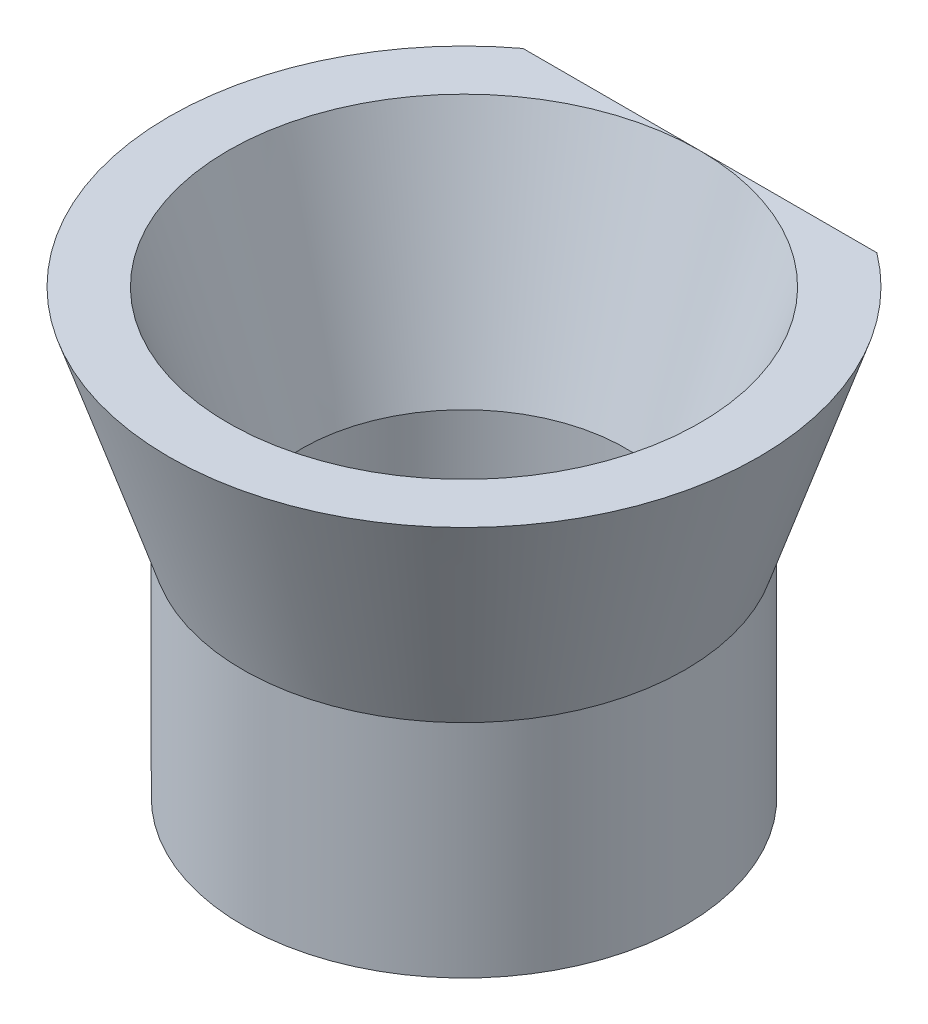
SolidWorks part; units mm, degrees
ref_plane "Alzado" through (0, 0, 0) normal (0, 0, 1) x (1, 0, 0)
ref_plane "Planta" through (0, 0, 0) normal (0, 1, 0) x (1, 0, 0)
ref_plane "Vista lateral" through (0, 0, 0) normal (1, 0, 0) x (0, 0, -1)
sketch "Croquis2" plane through (0, 0, 0) normal (0, 0, 1) x (1, 0, 0)
  line L0 (0, 0) -> (-5.5, 0) construction
  line L1 (-5.5, 0) -> (-8, 7.5)
  line L2 (-8, 7.5) -> (0, 7.5) construction
  line L3 (0, 7.5) -> (0, 0) construction
  line L4 (-8, 7.5) -> (-10, 7.5)
  line L5 (-10, 7.5) -> (-7.5, 0)
  line L6 (-7.5, 0) -> (-5.5, 0)
  dimension "D1" = 7.5
  dimension "D2" = 8
  dimension "D3" = 5.5
  dimension "D4" = 2
  dimension "D5" = 2
revolve "Revolución1" add sketch "Croquis2" angle 360 about L3
sketch "Croquis3" plane through (0, 0, 0) normal (0, -1, 0) x (1, 0, 0)
  circle A0 centre (0, 0) radius 5.5
  circle A1 centre (0, 0) radius 7.5
  dimension "D1" = 2
  dimension "D2" = 11
extrude "Saliente-Extruir1" add sketch "Croquis3" along normal blind 7.5
sketch "Croquis4" plane through (0, 7.5, 0) normal (0, 1, 0) x (1, 0, 0)
  line L0 (-7.3008, 8) -> (7.3008, 8)
  line L1 (7.3008, 8) -> (7.3008, 10.8672)
  line L2 (7.3008, 10.8672) -> (-7.3008, 10.8672)
  line L3 (-7.3008, 10.8672) -> (-7.3008, 8)
  point P3 (0, 8)
extrude "Cortar-Extruir1" cut sketch "Croquis4" against normal blind 19.5
